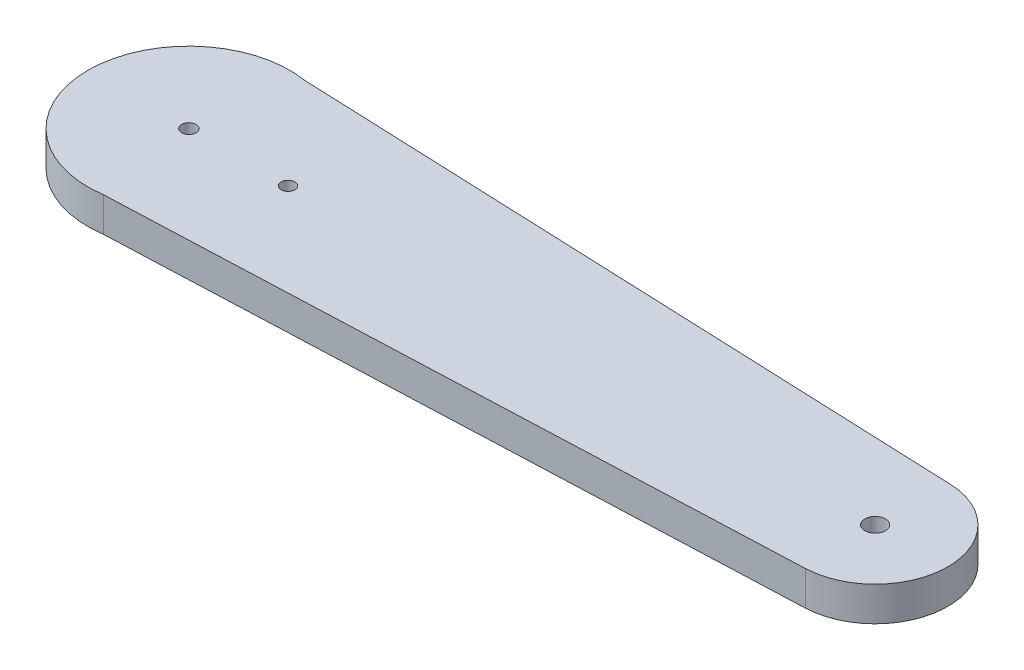
SolidWorks part; units mm, degrees
ref_plane "Front Plane" through (0, 0, 0) normal (0, 0, 1) x (1, 0, 0)
ref_plane "Top Plane" through (0, 0, 0) normal (0, 1, 0) x (1, 0, 0)
ref_plane "Right Plane" through (0, 0, 0) normal (1, 0, 0) x (0, 0, -1)
sketch "Sketch1" plane through (0, 0, 0) normal (0, 1, 0) x (1, 0, 0)
  line L5 (-52.7219, 0) -> (47.2781, 0) construction
  line L7 (-50.3488, 14.5275) -> (47.6312, 10.5941)
  line L8 (-50.5836, -14.5639) -> (47.7062, -10.5914)
  circle A0 centre (-52.7219, 0) radius 1.05
  arc A3 (-50.3488, 14.5275) -> (-50.5836, -14.5639) centre (-52.7219, 0) ccw
  circle A6 centre (47.2781, 0) radius 1.5
  arc A7 (47.7062, -10.5914) -> (47.6312, 10.5941) centre (47.2781, 0) ccw
  point P0 (0, 0)
  point P9 (62.5, 0)
  dimension "D1" = 100
  dimension "D2" = 2.1
  dimension "D3" = 3
  dimension "D4" = 10.6
  dimension "D5" = 14.72
extrude "Boss-Extrude1" add sketch "Sketch1" along normal blind 5
sketch "Sketch2" plane through (0, 5, 0) normal (0, 1, 0) x (1, 0, 0)
  circle A0 centre (-38.2719, 0) radius 1
  circle A1 centre (-52.7219, 0) radius 1.05 construction
  dimension "D1" = 2
  dimension "D2" = 14.45
extrude "Cut-Extrude1" cut sketch "Sketch2" against normal through all both and the other way through all
